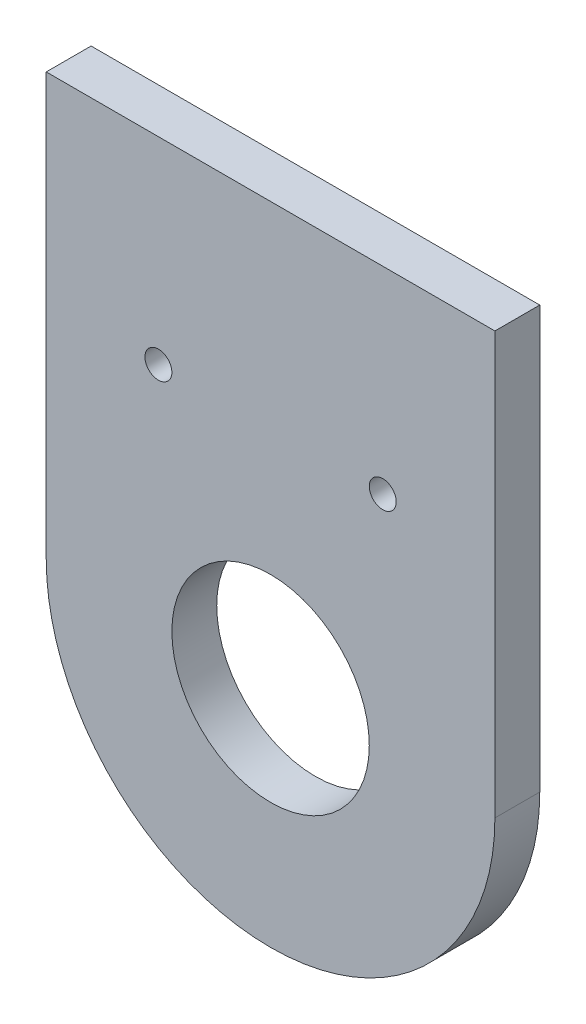
SolidWorks part; units mm, degrees
ref_plane "Plan de face" through (0, 0, 0) normal (0, 0, 1) x (1, 0, 0)
ref_plane "Plan de dessus" through (0, 0, 0) normal (0, 1, 0) x (1, 0, 0)
ref_plane "Plan de droite" through (0, 0, 0) normal (1, 0, 0) x (0, 0, -1)
sketch "Esquisse1" plane through (0, 0, 0) normal (0, 0, 1) x (1, 0, 0)
  line L0 (-47, 47) -> (47, 47)
  line L1 (-47, 47) -> (-47, -46.8078)
  line L2 (47, 47) -> (47, -46.8078)
  line L3 (-47, -46.8078) -> (47, -46.8078)
  circle A1 centre (0, 0) radius 11
extrude "Boss.-Extru.1" add sketch "Esquisse1" along normal blind 5
sketch "Esquisse2" plane through (0, 0, 5) normal (0, 0, 1) x (1, 0, 0)
  line L0 (-25, 0) -> (25, 0)
  line L1 (-25, 0) -> (-25, 50.4793)
  line L2 (25, 0) -> (25, 50.4793)
  line L3 (-25, 50.4793) -> (25, 50.4793)
  line L4 (-47, 47) -> (47, 47) construction
  circle A6 centre (0, 0) radius 25
  circle A7 centre (-12.5, 25) radius 1.5
  circle A8 centre (12.5, 25) radius 1.5
  point P4 (0, 0)
  point P12 (0, 0)
  point P33 (0, 0)
  dimension "D1" = 22
  dimension "D3" = 12.5
  dimension "D2" = 22
  dimension "D4" = 12.5
extrude "Enlèv. mat.-Extru.1" cut sketch "Esquisse2" against normal through all
